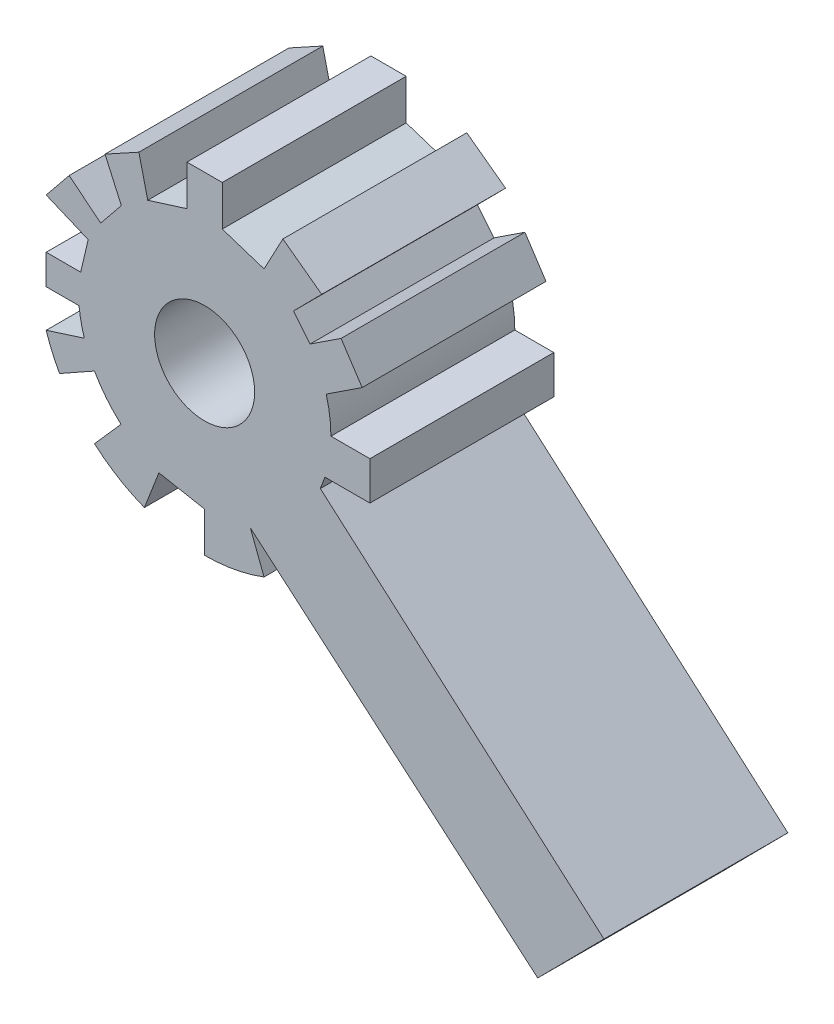
SolidWorks part; units mm, degrees
ref_plane "Front Plane" through (0, 0, 0) normal (0, 0, 1) x (1, 0, 0)
ref_plane "Top Plane" through (0, 0, 0) normal (0, 1, 0) x (1, 0, 0)
ref_plane "Right Plane" through (0, 0, 0) normal (1, 0, 0) x (0, 0, -1)
sketch "Sketch7" plane through (0, 0, 0) normal (0, 0, 1) x (1, 0, 0)
  line L157 (-110.2321, 18.9898) -> (-110.2321, 16.7942)
  line L158 (-103.5367, 13.7691) -> (-101.8565, 14.8745)
  line L159 (-104.442, 14.8745) -> (-102.9088, 16.4232)
  line L160 (-115.2616, 3.2145) -> (-113.819, 4.8479)
  line L161 (-116.6382, 15.1562) -> (-117.89, 13.6113)
  line L162 (-106.043, 1.545) -> (-106.8211, 3.5805)
  line L163 (-109.2732, 3.1278) -> (-109.2732, 0.9486)
  line L164 (-111.7596, 3.5938) -> (-112.5487, 1.5624)
  line L165 (-115.2616, 6.6342) -> (-117.1621, 5.5678)
  line L166 (-117.89, 7.2411) -> (-115.8142, 7.9044)
  line L167 (-117.89, 10.9165) -> (-117.89, 9.2905)
  line L168 (-117.89, 9.2905) -> (-116.1039, 9.2905)
  line L169 (-116.014, 10.9165) -> (-117.89, 10.9165)
  line L170 (-115.605, 12.6522) -> (-116.014, 10.9165)
  line L171 (-117.89, 13.6113) -> (-115.605, 12.6522)
  line L172 (-114.9262, 13.7691) -> (-116.6382, 15.1562)
  line L173 (-113.8022, 15.1562) -> (-114.9262, 13.7691)
  line L174 (-112.8488, 18.1481) -> (-114.6892, 17.1362)
  line L175 (-112.3687, 16.1243) -> (-112.8488, 18.1481)
  line L176 (-110.2321, 16.7942) -> (-112.3687, 16.1243)
  line L177 (-113.8022, 15.1562) -> (-114.6892, 17.1362)
  line L178 (-108.3143, 18.9898) -> (-110.2321, 18.9898)
  line L179 (-108.3143, 16.7942) -> (-108.3143, 18.9898)
  line L180 (-106.043, 16.0543) -> (-108.3143, 16.7942)
  line L181 (-105.0178, 17.9773) -> (-106.043, 16.0543)
  line L182 (-102.9088, 16.4232) -> (-105.0178, 17.9773)
  line L183 (-101.8565, 14.8745) -> (-100.7101, 13.1322)
  line L184 (-100.7101, 13.1322) -> (-102.6613, 11.8484)
  line L185 (-102.4063, 9.9947) -> (-100.287, 9.9947)
  line L186 (-100.287, 9.9947) -> (-100.287, 7.9044)
  line L187 (-100.287, 7.9044) -> (-102.7322, 7.9044)
  line L188 (-91.1619, -9.898) -> (-106.8712, 3.5616)
  line L189 (-87.561, -6.2608) -> (-91.1619, -9.898)
  line L190 (-102.9826, 7.2411) -> (-87.561, -6.2608)
  line L191 (-111.7596, 3.5938) -> (-109.2732, 3.1278)
  line L192 (-104.442, 14.8745) -> (-103.5367, 13.7691)
  line L193 (-102.9826, 7.2411) -> (-102.7322, 7.9044)
  arc A34 (-115.8142, 7.9044) -> (-116.1039, 9.2905) centre (-109.2732, 9.9947) cw
  arc A35 (-117.1621, 5.5678) -> (-117.89, 7.2411) centre (-109.2732, 9.9947) cw
  arc A36 (-106.043, 1.545) -> (-109.2732, 0.9486) centre (-109.2732, 9.9947) cw
  arc A37 (-112.5487, 1.5624) -> (-115.2616, 3.2145) centre (-109.2732, 9.9947) cw
  arc A38 (-113.819, 4.8479) -> (-115.2616, 6.6342) centre (-109.2732, 9.9947) cw
  arc A39 (-102.6613, 11.8484) -> (-102.4063, 9.9947) centre (-109.2732, 9.9947) cw
  circle A40 centre (-109.2732, 9.9947) radius 0.9019
  circle A41 centre (-109.2732, 9.9947) radius 2.719
  point P20 (-87.0696, 24.2196)
  point P181 (-102.9826, 7.2411)
extrude "Boss-Extrude5" add sketch "Sketch7" along normal mid plane 10
